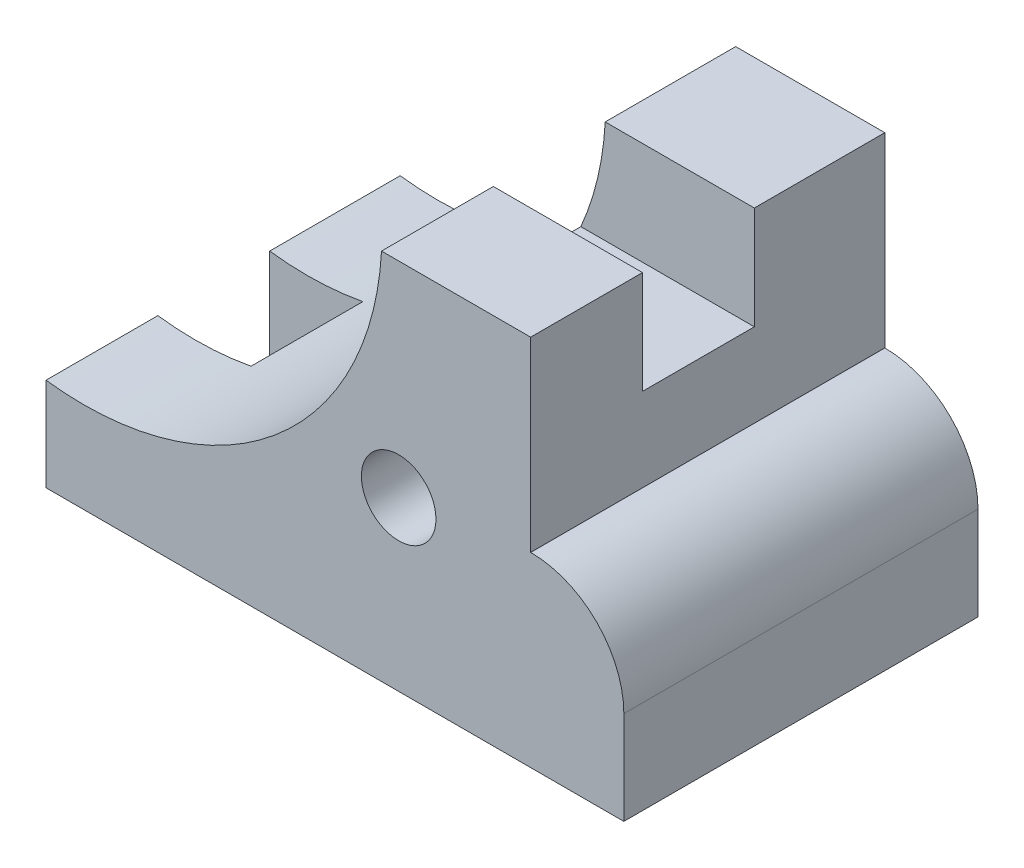
SolidWorks part; units mm, degrees
material "Cedar"
ref_plane "Front Plane" through (0, 0, 0) normal (0, 0, 1) x (1, 0, 0)
ref_plane "Top Plane" through (0, 0, 0) normal (0, 1, 0) x (1, 0, 0)
ref_plane "Right Plane" through (0, 0, 0) normal (1, 0, 0) x (0, 0, -1)
sketch "Sketch1" plane through (0, 0, 0) normal (0, 0, 1) x (1, 0, 0)
  line L1 (0, 0) -> (82.55, 0)
  line L2 (0, 0) -> (0, 15.875)
  line L3 (57.15, 63.5) -> (82.55, 63.5)
  line L4 (82.55, 31.75) -> (82.55, 63.5)
  line L5 (82.55, 0) -> (98.425, 0)
  line L7 (82.55, 31.75) -> (82.5754, 31.75)
  line L8 (98.425, 0) -> (98.425, 15.9004)
  arc A0 (0, 15.875) -> (57.15, 63.5) centre (6.4272, 66.2649) ccw
  arc A1 (82.5754, 31.75) -> (98.425, 15.9004) centre (82.5754, 15.9004) cw
  point P12 (98.425, 31.75)
  dimension "D7" = 15.875
  dimension "D1" = 82.55
  dimension "D2" = 63.5
  dimension "D3" = 15.875
  dimension "D4" = 25.4
  dimension "D5" = 15.875
  dimension "D6" = 31.75
extrude "Boss-Extrude1" add sketch "Sketch1" against normal blind 60.325
sketch "Sketch2" plane through (82.55, 0, 0) normal (1, 0, 0) x (0, 0, -1)
  line L0 (60.325, 63.5) -> (0, 63.5) construction
  line L1 (19.05, 63.5) -> (38.1, 63.5)
  line L2 (19.05, 63.5) -> (19.05, 45.974)
  line L3 (19.05, 45.974) -> (38.1, 45.974)
  line L4 (38.1, 63.5) -> (38.1, 45.974)
  dimension "D1" = 17.526
  dimension "D2" = 19.05
  dimension "D3" = 19.05
extrude "Cut-Extrude1" cut sketch "Sketch2" against normal blind 29.8196 contours L2 L1 L4 L3
sketch "Sketch3" plane through (0, 0, 0) normal (0, -1, 0) x (1, 0, 0)
  line L0 (0, -60.325) -> (0, 0) construction
  line L1 (0, -38.1) -> (15.875, -38.1)
  line L2 (0, -38.1) -> (0, -19.05)
  line L3 (0, -19.05) -> (15.875, -19.05)
  line L4 (15.875, -38.1) -> (15.875, -19.05)
  dimension "D1" = 15.875
  dimension "D2" = 19.05
  dimension "D3" = 19.05
extrude "Cut-Extrude2" cut sketch "Sketch3" against normal blind 29.8196 contours L2 L1 L4 L3
sketch "Sketch4" plane through (0, 0, 0) normal (0, 0, 1) x (1, 0, 0)
  line L0 (0, 0) -> (98.425, 0) construction
  circle A0 centre (60.071, 28.575) radius 6.35
  point P6 (60.9392, 27.1718)
  dimension "D1" = 12.7
  dimension "D2" = 28.575
  dimension "D3" = 38.354
extrude "Cut-Extrude3" cut sketch "Sketch4" against normal blind 60.3504 contours A0
